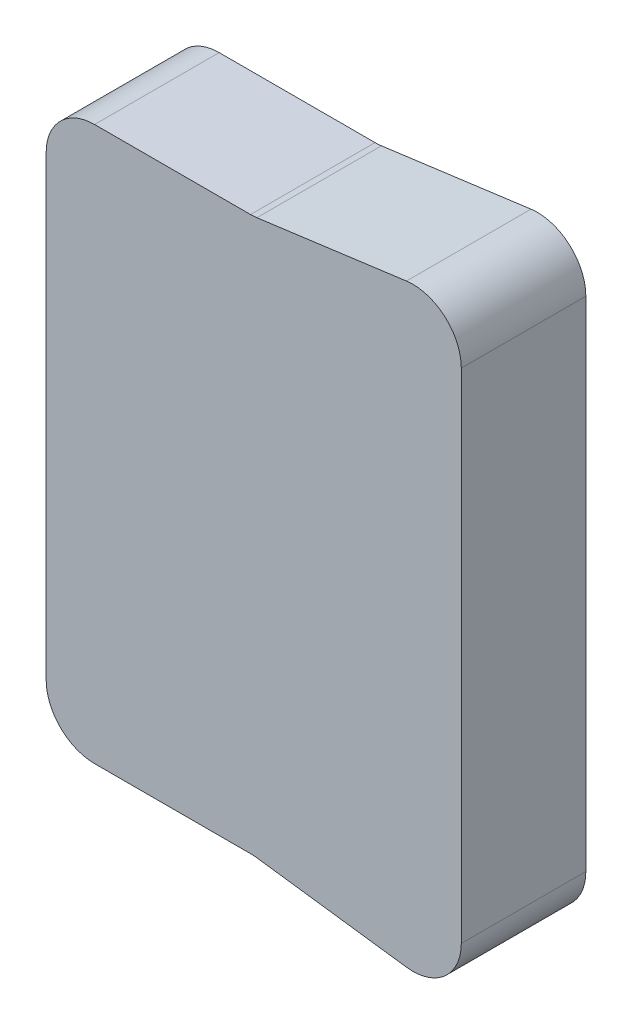
SolidWorks part; units mm, degrees
ref_plane "Front Plane" through (0, 0, 0) normal (0, 0, 1) x (1, 0, 0)
ref_plane "Top Plane" through (0, 0, 0) normal (0, 1, 0) x (1, 0, 0)
ref_plane "Right Plane" through (0, 0, 0) normal (1, 0, 0) x (0, 0, -1)
sketch "Sketch1" plane through (0, 0, 0) normal (0, 0, 1) x (1, 0, 0)
  line L0 (0, 80) -> (0, 0)
  line L1 (0, 0) -> (30, 0)
  line L2 (30, 0) -> (60, -4)
  line L3 (60, -4) -> (60, 84)
  line L4 (30, 0) -> (60, 0) construction
  line L5 (30, 80) -> (60, 84)
  line L6 (0, 40) -> (60, 40) construction
  line L7 (0, 80) -> (30, 80)
  point P1 (30, 40)
  dimension "D1" = 4
  dimension "D2" = 80
  dimension "D3" = 60
extrude "Boss-Extrude1" add sketch "Sketch1" along normal blind 18 contours L7 L5 L3 L2 L1 L0
fillet "Fillet1" radius 7 6 edges at (30, 0, 9) (30, 80, 9) (0, 0, 9) (60, -4, 9) (60, 84, 9) (0, 80, 9)
equation "\"tool_diameter\"=9"
equation "\"hole_clearance\"=0.5"
equation "\"material_thickness\"=18"
equation "\"clearance\"=0.5"
equation "\"outer_slot\"=0.5"
equation "\"fillet\"=7"
equation "\"D1@Boss-Extrude1\"=\"material_thickness\""
equation "\"D1@Fillet1\"=\"fillet\""
